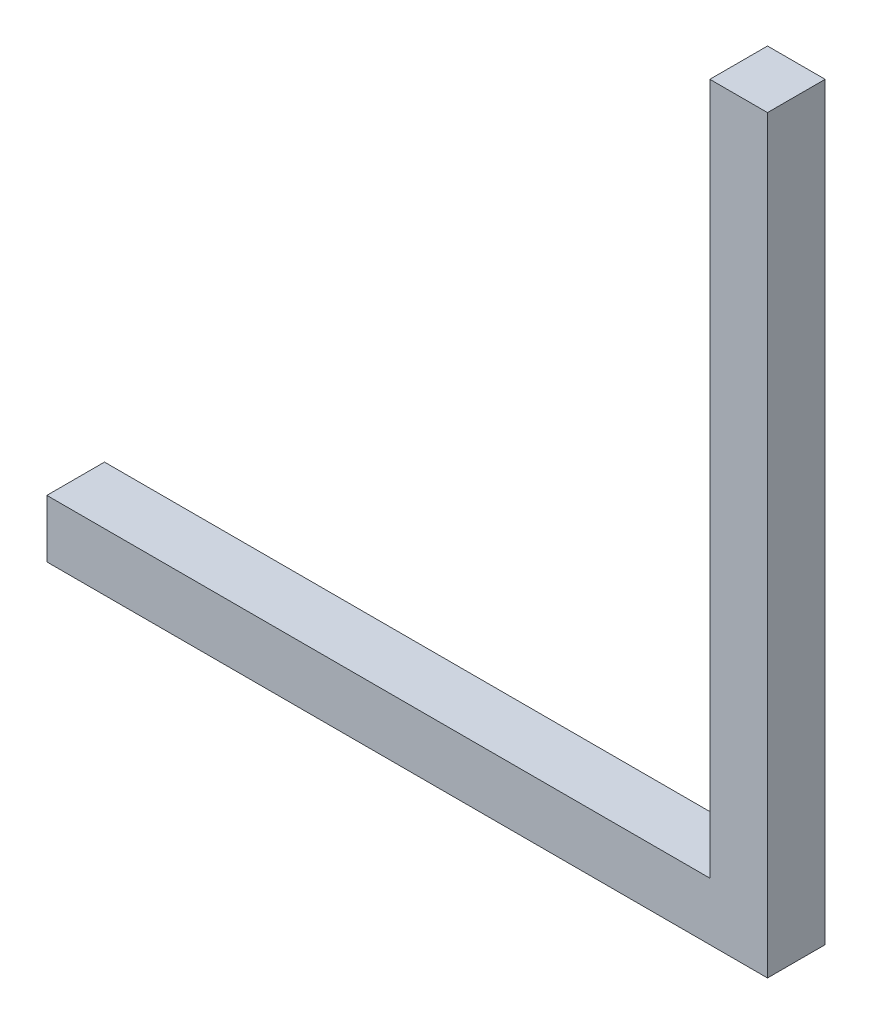
SolidWorks part; units mm, degrees
ref_plane "Plan de face" through (0, 0, 0) normal (0, 0, 1) x (1, 0, 0)
ref_plane "Plan de dessus" through (0, 0, 0) normal (0, 1, 0) x (1, 0, 0)
ref_plane "Plan de droite" through (0, 0, 0) normal (1, 0, 0) x (0, 0, -1)
sketch "Esquisse1" plane through (0, 0, 0) normal (0, 0, 1) x (1, 0, 0)
  line L1 (-18.4372, 14.3171) -> (96.5628, 14.3171)
  line L2 (-18.4372, 14.3171) -> (-18.4372, 4.3171)
  line L3 (-18.4372, 4.3171) -> (96.5628, 4.3171)
  line L4 (96.5628, 14.3171) -> (96.5628, 4.3171)
  dimension "D1" = 115
  dimension "D2" = 10
extrude "Boss.-Extru.1" add sketch "Esquisse1" along normal blind 10
sketch "Esquisse2" plane through (96.5628, 0, 0) normal (1, 0, 0) x (0, 0, -1)
  line L1 (0, 4.3171) -> (-10, 4.3171)
  line L2 (0, 4.3171) -> (0, 134.3171)
  line L3 (0, 134.3171) -> (-10, 134.3171)
  line L4 (-10, 4.3171) -> (-10, 134.3171)
  dimension "D1" = 10
  dimension "D2" = 130
extrude "Boss.-Extru.2" add sketch "Esquisse2" along normal blind 10
